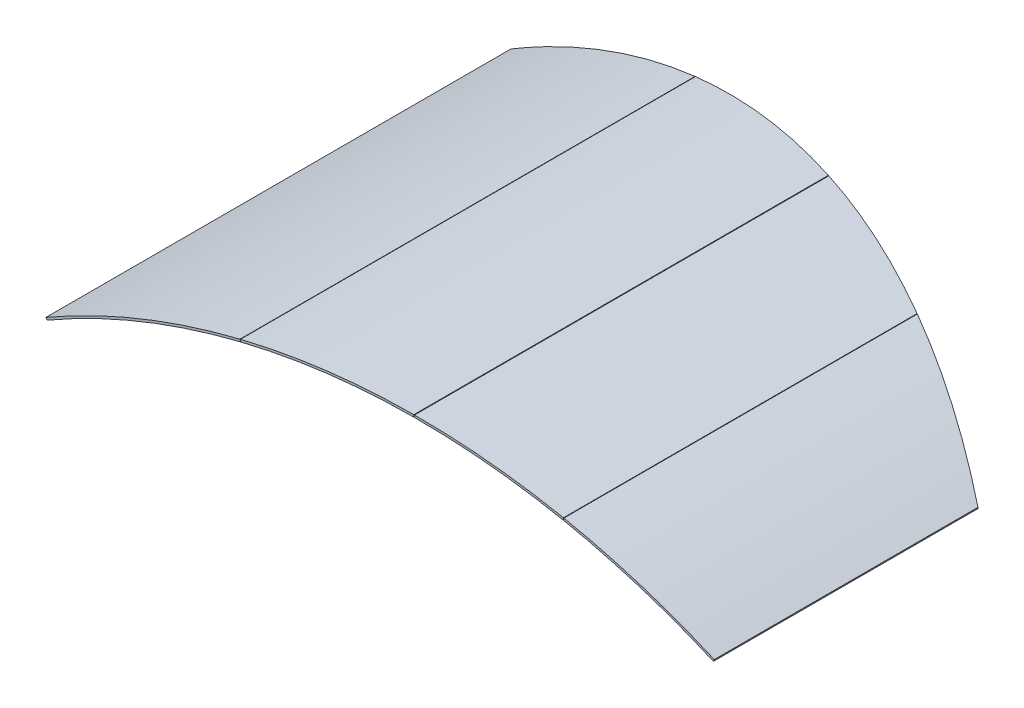
SolidWorks part; units mm, degrees
material "PC High Viscosity"
ref_plane "Front Plane" through (0, 0, 0) normal (0, 0, 1) x (1, 0, 0)
ref_plane "Top Plane" through (0, 0, 0) normal (0, 1, 0) x (1, 0, 0)
ref_plane "Right Plane" through (0, 0, 0) normal (1, 0, 0) x (0, 0, -1)
sketch "Sketch1" plane through (0, 0, 0) normal (0, 0, 1) x (1, 0, 0)
  line L0 (-18789.6368, -394.476) -> (-18799.1067, -417.613) construction
  line L1 (-23335.2514, -652.8819) -> (-23342.7581, -639.8954)
  line L2 (-18790.1235, -395.6651) -> (-18784.1298, -381.9146)
  line L3 (-19813.0954, -73.97) -> (-19810.1403, -59.264)
  line L4 (-20829.1946, 24.9555) -> (-20829.1946, 39.9556)
  line L5 (-19813.0954, -58.6711) -> (-19816.0417, -73.3789)
  line L6 (-20833.9484, 24.9332) -> (-20833.9484, 39.9334)
  line L7 (-22016.1671, -121.655) -> (-22019.7557, -107.0906)
  line L9 (-22016.338, -106.2497) -> (-22012.7494, -120.8141)
  arc A0 (-23335.2514, -652.8819) -> (-22016.1671, -121.655) centre (-20807.9834, -5025) cw
  arc A1 (-23342.7581, -639.8954) -> (-22019.7557, -107.0906) centre (-20807.9834, -5025) cw
  arc A2 (-19810.1403, -59.264) -> (-18784.1298, -381.9146) centre (-20807.9834, -5025) cw
  arc A3 (-23342.7581, -639.8954) -> (-18784.1298, -381.9146) centre (-20807.9834, -5025) cw construction
  arc A4 (-19813.0954, -73.97) -> (-18790.1235, -395.6651) centre (-20807.9834, -5025) cw
  arc A5 (-23335.2514, -652.8819) -> (-18790.1235, -395.6651) centre (-20807.9834, -5025) cw construction
  arc A6 (-20829.1946, 39.9556) -> (-19813.0954, -58.6711) centre (-20807.9834, -5025) cw
  arc A7 (-20829.1946, 24.9555) -> (-19816.0417, -73.3789) centre (-20807.9834, -5025) cw
  arc A8 (-22016.338, -106.2497) -> (-20833.9484, 39.9334) centre (-20807.9834, -5025) cw
  arc A9 (-22012.7494, -120.8141) -> (-20833.9484, 24.9332) centre (-20807.9834, -5025) cw
  dimension "D1" = 15
extrude "Boss-Extrude1" add sketch "Sketch1" against normal up to surface (3583.6944 mm away)
sketch "Sketch2" plane through (-13215.7696, -9495.4166, 12327.336) normal (-0.0565, 0.9984, 0) x (-0.9984, -0.0565, 0)
  line L0 (4915.9753, -14030.3048) -> (4915.9753, -16551.9624)
  line L1 (4915.9753, -16551.9624) -> (9934.4451, -16551.9624)
  line L2 (9934.4451, -16551.9624) -> (9934.4451, -15483.3306)
  line L3 (9934.4451, -15483.3306) -> (9864.4613, -15483.3306)
  arc A0 (4915.9753, -14030.3048) -> (9864.4613, -15483.3306) centre (9292.5752, -8278.0705) ccw
extrude "Cut-Extrude1" cut sketch "Sketch2" along normal through all
